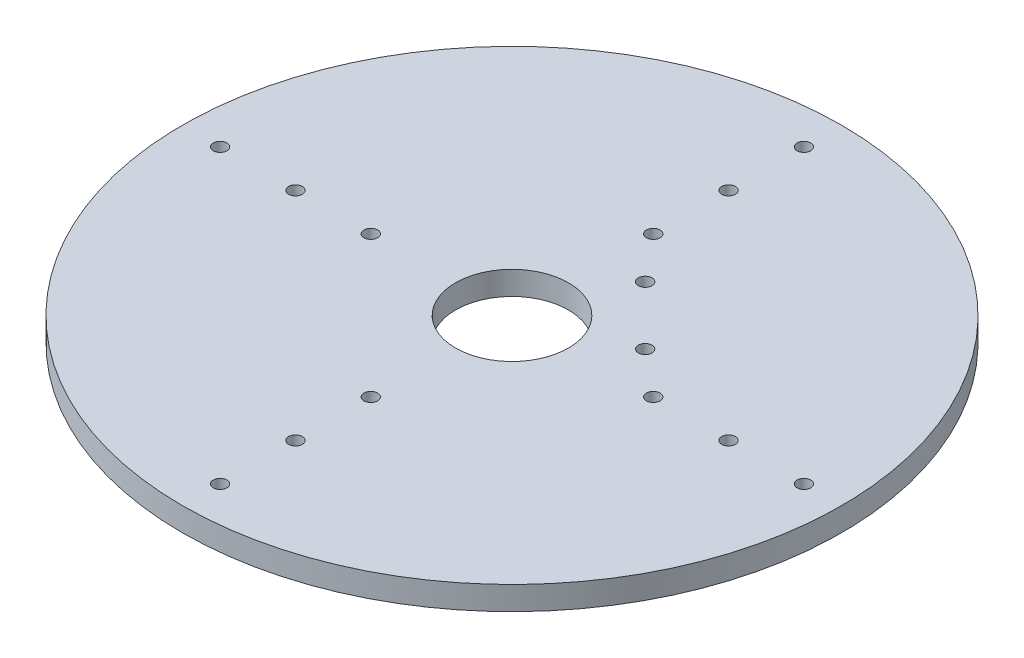
SolidWorks part; units mm, degrees
ref_plane "前视基准面" through (0, 0, 0) normal (0, 0, 1) x (1, 0, 0)
ref_plane "上视基准面" through (0, 0, 0) normal (0, 1, 0) x (1, 0, 0)
ref_plane "右视基准面" through (0, 0, 0) normal (1, 0, 0) x (0, 0, -1)
sketch "草图1" plane through (0, 0, 0) normal (0, 1, 0) x (1, 0, 0)
  circle A0 centre (0, 0) radius 70
  circle A1 centre (7.955, 20.3293) radius 1.45
  circle A2 centre (20.3293, 7.955) radius 1.45
  circle A3 centre (0, 0) radius 12
  circle A4 centre (30, 0) radius 1.45
  circle A5 centre (46, 0) radius 1.45
  circle A6 centre (62, 0) radius 1.45
  circle A7 centre (0, 30) radius 1.45
  circle A8 centre (0, 46) radius 1.45
  circle A9 centre (0, 62) radius 1.45
  circle A10 centre (-30, 0) radius 1.45
  circle A11 centre (-46, 0) radius 1.45
  circle A12 centre (-62, 0) radius 1.45
  circle A13 centre (0, -30) radius 1.45
  circle A14 centre (0, -46) radius 1.45
  circle A15 centre (0, -62) radius 1.45
extrude "凸台-拉伸1" add sketch "草图1" along normal mid plane 5
